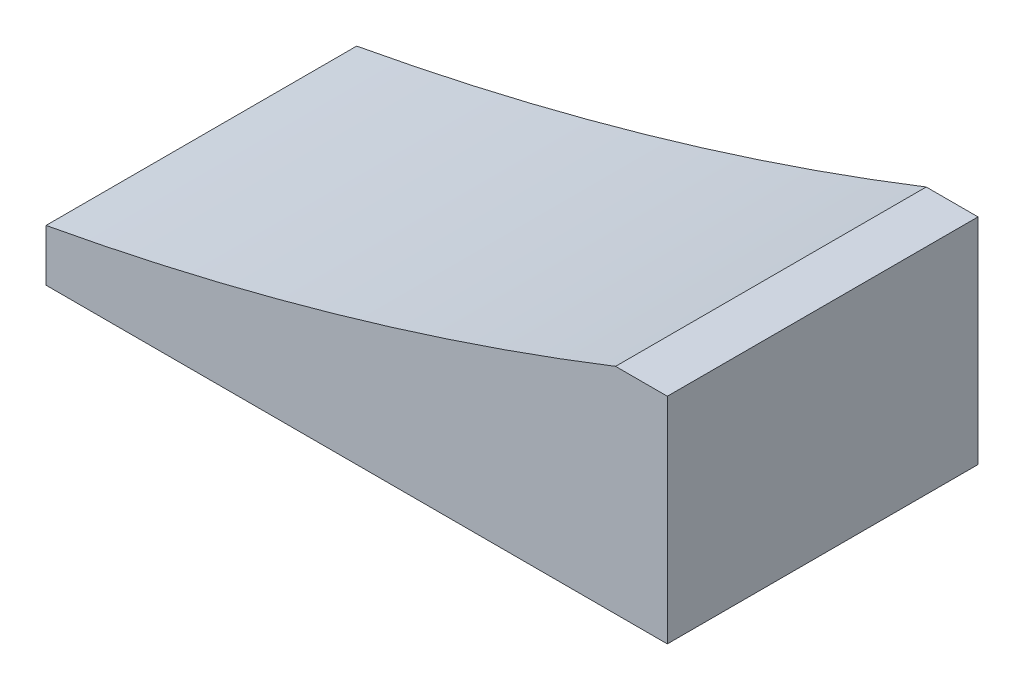
SolidWorks part; units mm, degrees
ref_plane "Front Plane" through (0, 0, 0) normal (0, 0, 1) x (1, 0, 0)
ref_plane "Top Plane" through (0, 0, 0) normal (0, 1, 0) x (1, 0, 0)
ref_plane "Right Plane" through (0, 0, 0) normal (1, 0, 0) x (0, 0, -1)
sketch "Sketch2" plane through (0, 0, 0) normal (0, 0, 1) x (1, 0, 0)
  line L0 (0, -300) -> (114.5436, -300)
  line L1 (114.5436, -300) -> (114.5436, -277.272)
  line L2 (54.5436, -295) -> (54.5436, -300)
  line L3 (114.5436, -279.2852) -> (109.5436, -279.2852)
  circle A0 centre (0, 0) radius 300 construction
  arc A1 (0, -300) -> (114.5436, -277.272) centre (0, 0) ccw
  dimension "D1" = 600
  dimension "D3" = 5
  dimension "D2" = 60
  dimension "D4" = 5
extrude "Boss-Extrude1" add sketch "Sketch2" along normal blind 30 contours A1 L0 L1
